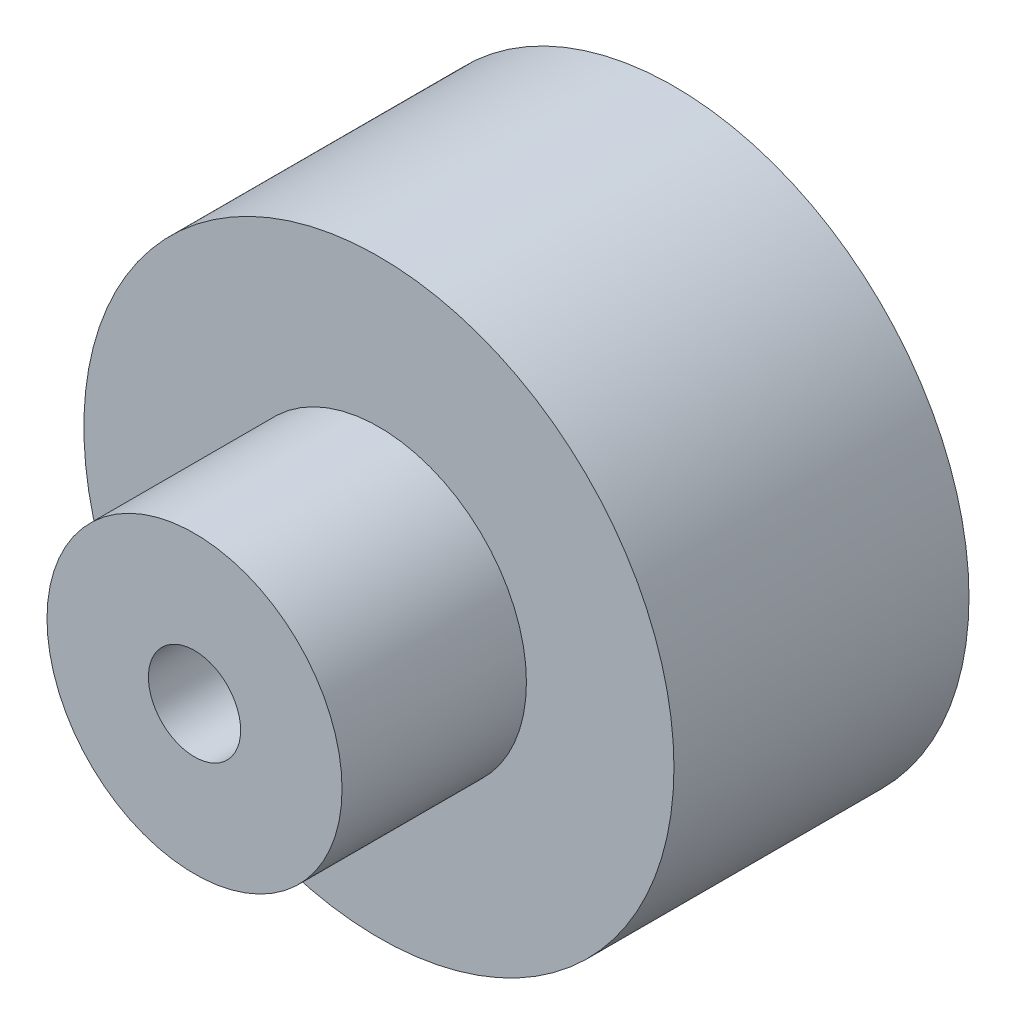
SolidWorks part; units mm, degrees
material "Brass"
ref_plane "Front Plane" through (0, 0, 0) normal (0, 0, 1) x (1, 0, 0)
ref_plane "Top Plane" through (0, 0, 0) normal (0, 1, 0) x (1, 0, 0)
ref_plane "Right Plane" through (0, 0, 0) normal (1, 0, 0) x (0, 0, -1)
sketch "Sketch1" plane through (0, 0, 0) normal (0, 0, 1) x (1, 0, 0)
  circle A0 centre (0, 0) radius 8
  dimension "D1" = 16
extrude "Boss-Extrude1" add sketch "Sketch1" along normal blind 8
sketch "Sketch2" plane through (0, 0, 8) normal (0, 0, 1) x (1, 0, 0)
  circle A0 centre (0, 0) radius 4
  dimension "D1" = 8
extrude "Boss-Extrude2" add sketch "Sketch2" along normal blind 5
sketch "Sketch4" plane through (0, 0, 13) normal (0, 0, 1) x (1, 0, 0)
  point P0 (0, 0)
hole_wizard "M3 Tapped Hole1" positions "3DSketch4" profile "Sketch6" tap size "M3" standard "DIN"
sketch3d "3DSketch4"
  point P0 (0, 0, 13)
sketch "Sketch6" plane through (0, 0, 13) normal (1, 0, 0) x (0, -1, 0)
  line L0 (0, 0) -> (0, 9.2511)
  line L1 (0, 9.2511) -> (1.25, 8.5)
  line L2 (1.25, 8.5) -> (1.25, 0)
  line L5 (1.25, 0) -> (0, 0)
  line L10 (0, 9.2511) -> (-1.25, 8.5) construction
  line L11 (0, -6.35) -> (0, 107.95) construction
  dimension "Tap Drill Dia." = 2.5
  dimension "Tap Drill Depth" = 8.5
  dimension "Drill Angle" = 118
cosmetic thread "Hole Thread1" parameters "D1"=6, "D2"=3
